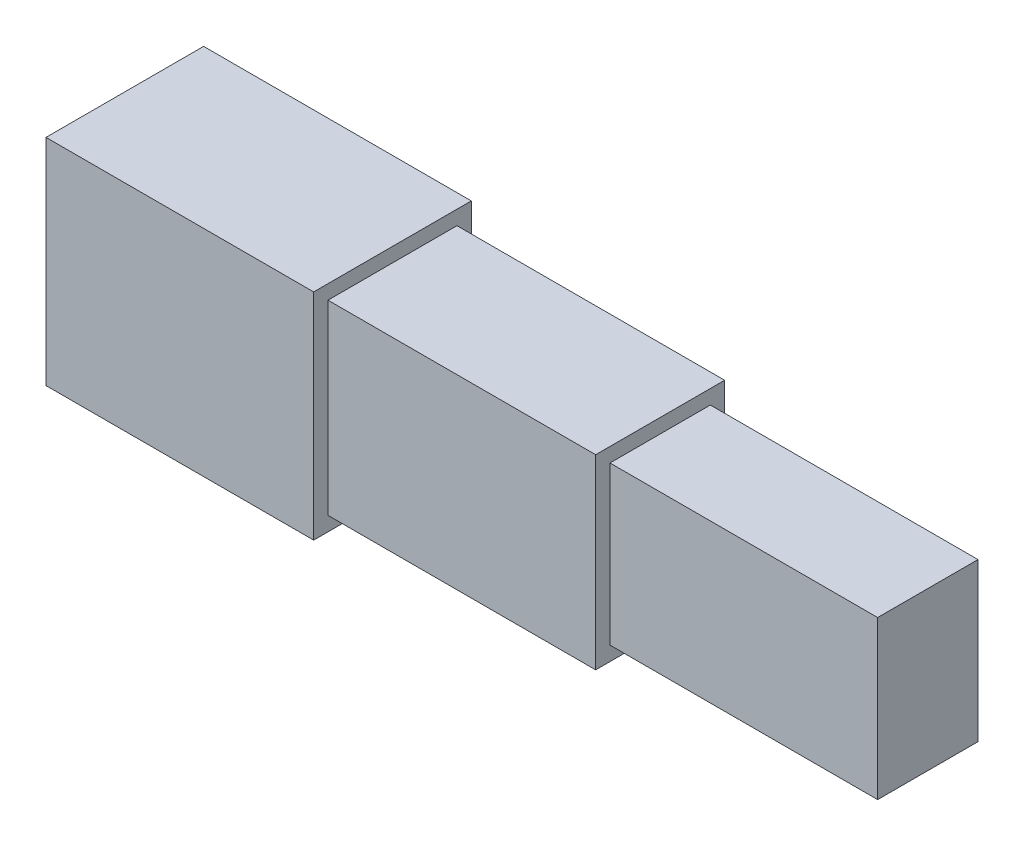
SolidWorks part; units mm, degrees
ref_plane "Front Plane" through (0, 0, 0) normal (0, 0, 1) x (1, 0, 0)
ref_plane "Top Plane" through (0, 0, 0) normal (0, 1, 0) x (1, 0, 0)
ref_plane "Right Plane" through (0, 0, 0) normal (1, 0, 0) x (0, 0, -1)
sketch "Sketch1" plane through (0, 0, 0) normal (1, 0, 0) x (0, 0, -1)
  line L1 (-274.8155, -374.8155) -> (274.8155, -374.8155)
  line L2 (-274.8155, -374.8155) -> (-274.8155, 374.8155)
  line L3 (-274.8155, 374.8155) -> (274.8155, 374.8155)
  line L4 (274.8155, -374.8155) -> (274.8155, 374.8155)
  line L5 (-274.8155, -374.8155) -> (274.8155, 374.8155) construction
  line L6 (-274.8155, 374.8155) -> (274.8155, -374.8155) construction
  point P0 (0, 0)
  dimension "D1" = 549.631
  dimension "D2" = 749.631
extrude "Boss-Extrude1" add sketch "Sketch1" along normal blind 933.3333
sketch "Sketch2" plane through (933.3333, 0, 0) normal (1, 0, 0) x (0, 0, -1)
  line L1 (-224.9, -324.9) -> (224.9, -324.9)
  line L2 (-224.9, -324.9) -> (-224.9, 324.9)
  line L3 (-224.9, 324.9) -> (224.9, 324.9)
  line L4 (224.9, -324.9) -> (224.9, 324.9)
  line L5 (-224.9, -324.9) -> (224.9, 324.9) construction
  line L6 (-224.9, 324.9) -> (224.9, -324.9) construction
  point P0 (0, 0)
  dimension "D1" = 449.8
  dimension "D2" = 649.8
extrude "Boss-Extrude2" add sketch "Sketch2" along normal blind 933.3333
sketch "Sketch3" plane through (1866.6667, 0, 0) normal (1, 0, 0) x (0, 0, -1)
  line L1 (-174.9845, -274.9845) -> (174.9845, -274.9845)
  line L2 (-174.9845, -274.9845) -> (-174.9845, 274.9845)
  line L3 (-174.9845, 274.9845) -> (174.9845, 274.9845)
  line L4 (174.9845, -274.9845) -> (174.9845, 274.9845)
  line L5 (-174.9845, -274.9845) -> (174.9845, 274.9845) construction
  line L6 (-174.9845, 274.9845) -> (174.9845, -274.9845) construction
  point P0 (0, 0)
  dimension "D1" = 349.969
  dimension "D2" = 549.969
extrude "Boss-Extrude3" add sketch "Sketch3" along normal blind 933.3333
